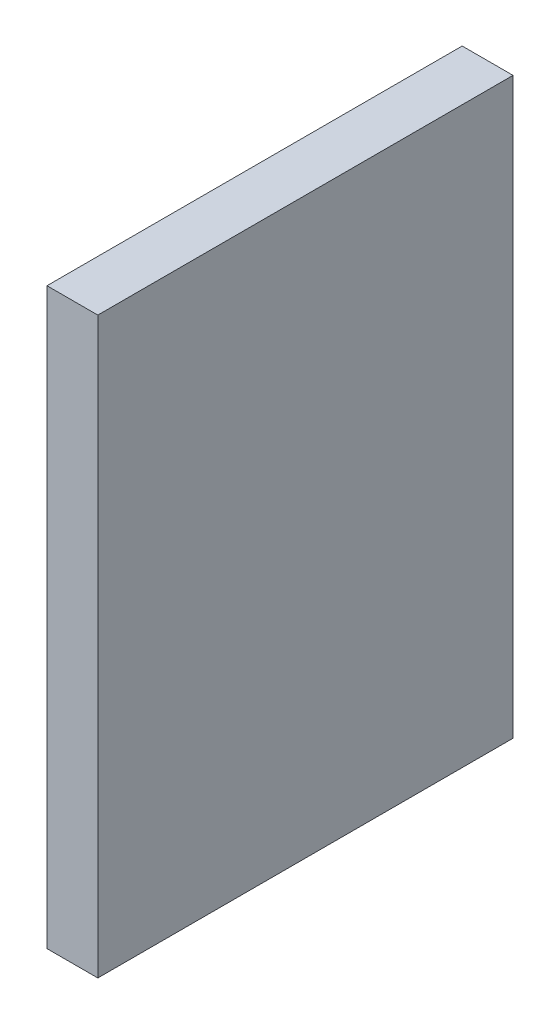
SolidWorks part; units mm, degrees
ref_plane "Front Plane" through (0, 0, 0) normal (0, 0, 1) x (1, 0, 0)
ref_plane "Top Plane" through (0, 0, 0) normal (0, 1, 0) x (1, 0, 0)
ref_plane "Right Plane" through (0, 0, 0) normal (1, 0, 0) x (0, 0, -1)
sketch "Sketch1" plane through (0, 0, 0) normal (1, 0, 0) x (0, 0, -1)
  line L0 (16.5384, -22.8367) -> (16.5384, -56.7137) construction
  line L1 (16.5384, -56.7137) -> (41.0384, -56.7137)
  line L2 (16.5384, -56.7137) -> (16.5384, -22.8367)
  line L3 (16.5384, -22.8367) -> (41.0384, -22.8367)
  line L4 (41.0384, -56.7137) -> (41.0384, -22.8367)
  point P0 (0, 0)
extrude "Boss-Extrude1" add sketch "Sketch1" along normal blind 3
